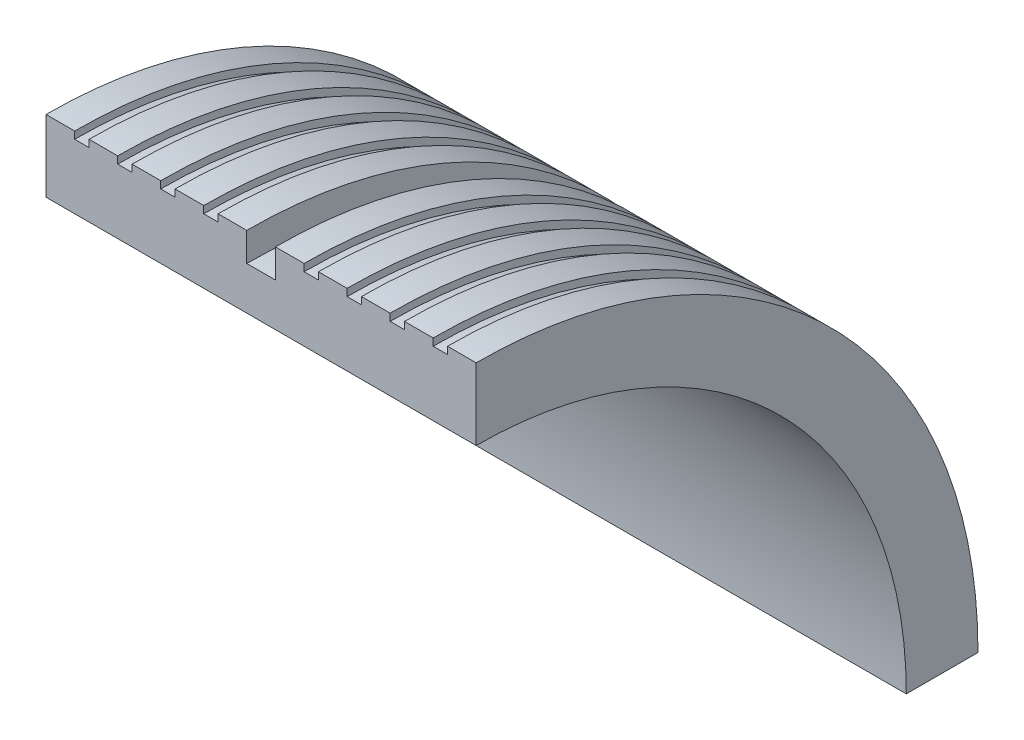
SolidWorks part; units mm, degrees
ref_plane "Front Plane" through (0, 0, 0) normal (0, 0, 1) x (1, 0, 0)
ref_plane "Top Plane" through (0, 0, 0) normal (0, 1, 0) x (1, 0, 0)
ref_plane "Right Plane" through (0, 0, 0) normal (1, 0, 0) x (0, 0, -1)
sketch "Sketch1" plane through (0, 0, 0) normal (1, 0, 0) x (0, 0, -1)
  line L0 (0, 35) -> (0, 30)
  line L1 (35, 0) -> (30, 0)
  arc A0 (0, 35) -> (35, 0) centre (0, 0) cw
  arc A1 (0, 30) -> (30, 0) centre (0, 0) cw
  dimension "D1" = 35
  dimension "D2" = 5
extrude "Boss-Extrude1" add sketch "Sketch1" along normal blind 30
sketch "Sketch2" plane through (0, 0, 0) normal (0, 0, 1) x (1, 0, 0)
  line L0 (30, 35) -> (0, 35) construction
  line L1 (30, 35) -> (0, 35) construction
  line L2 (0, 35) -> (0, 30) construction
  line L3 (2, 34.5) -> (3, 34.5)
  line L4 (2, 34.5) -> (2, 35.5)
  line L5 (2, 35.5) -> (3, 35.5)
  line L6 (3, 34.5) -> (3, 35.5)
  line L7 (2, 34.5) -> (3, 35.5) construction
  line L8 (2, 35.5) -> (3, 34.5) construction
  line L13 (5, 34.5) -> (5, 35.5)
  line L14 (5, 34.5) -> (6, 34.5)
  line L15 (6, 34.5) -> (6, 35.5)
  line L16 (5, 35.5) -> (6, 35.5)
  line L17 (8, 34.5) -> (8, 35.5)
  line L18 (8, 34.5) -> (9, 34.5)
  line L19 (9, 34.5) -> (9, 35.5)
  line L20 (8, 35.5) -> (9, 35.5)
  line L21 (11, 34.5) -> (11, 35.5)
  line L22 (11, 34.5) -> (12, 34.5)
  line L23 (12, 34.5) -> (12, 35.5)
  line L24 (11, 35.5) -> (12, 35.5)
  line L25 (2, 34.5) -> (5, 34.5) construction
  line L26 (15, 35) -> (15, 25.6626) construction
  line L27 (28, 35.5) -> (27, 34.5) construction
  line L28 (28, 34.5) -> (27, 35.5) construction
  line L29 (19, 35.5) -> (18, 35.5)
  line L30 (18, 34.5) -> (18, 35.5)
  line L31 (19, 34.5) -> (18, 34.5)
  line L32 (19, 34.5) -> (19, 35.5)
  line L33 (22, 35.5) -> (21, 35.5)
  line L34 (21, 34.5) -> (21, 35.5)
  line L35 (22, 34.5) -> (21, 34.5)
  line L36 (22, 34.5) -> (22, 35.5)
  line L37 (25, 35.5) -> (24, 35.5)
  line L38 (24, 34.5) -> (24, 35.5)
  line L39 (25, 34.5) -> (24, 34.5)
  line L40 (25, 34.5) -> (25, 35.5)
  line L41 (27, 34.5) -> (27, 35.5)
  line L42 (28, 35.5) -> (27, 35.5)
  line L43 (28, 34.5) -> (28, 35.5)
  line L44 (28, 34.5) -> (27, 34.5)
  line L46 (14, 33) -> (16, 33)
  line L47 (14, 33) -> (14, 35)
  line L48 (14, 35) -> (16, 35)
  line L49 (16, 33) -> (16, 35)
  line L50 (14, 33) -> (16, 35) construction
  line L51 (14, 35) -> (16, 33) construction
  point P2 (2.5, 35)
  point P41 (27.5, 35)
  point P46 (15, 35)
  dimension "D1" = 1
  dimension "D2" = 4
  dimension "D3" = 2
  dimension "D4" = 3
  dimension "D5" = 2
ref_axis "Axis1" through (30, 0, 0) along (-1, 0, 0)
revolve "Cut-Revolve1" cut sketch "Sketch2" angle 360 about axis through (30, 0, 0) along (-1, 0, 0)
